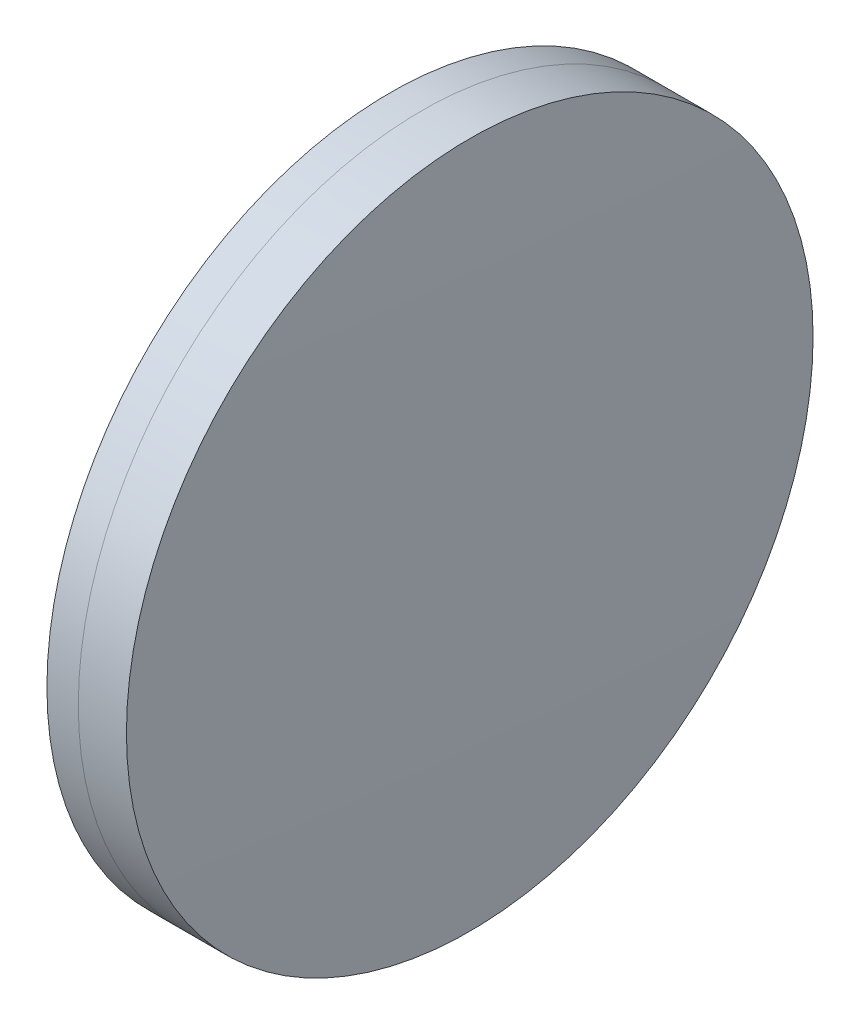
SolidWorks part; units mm, degrees
ref_plane "前视基准面" through (0, 0, 0) normal (0, 0, 1) x (1, 0, 0)
ref_plane "上视基准面" through (0, 0, 0) normal (0, 1, 0) x (1, 0, 0)
ref_plane "右视基准面" through (0, 0, 0) normal (1, 0, 0) x (0, 0, -1)
sketch "草图1" plane through (0, 0, 0) normal (0, 1, 0) x (1, 0, 0)
  line L0 (124.5233, 0) -> (746.023, 0) construction
  line L1 (713.6122, -25.4) -> (715.934, -25.4)
  line L2 (713.6122, 25.4) -> (715.934, 25.4)
  arc A0 (715.934, -25.4) -> (715.934, 25.4) centre (457.7806, 0) ccw
  arc A1 (713.6122, 25.4) -> (713.6122, -25.4) centre (1059.3806, 0) ccw
  point P4 (746.023, 0)
  point P10 (712.6806, 0)
  point P11 (717.1806, 0)
  dimension "D3" = 346.7
  dimension "D4" = 259.4
  dimension "D1" = 25.4
  dimension "D2" = 25.4
  dimension "D5" = 4.5
revolve "旋转1" add sketch "草图1" angle 360 about L0
sketch "草图2" plane through (0, 0, 0) normal (0, 1, 0) x (1, 0, 0)
  line L0 (-0.5519, 0) -> (779.9324, 0) construction
  line L2 (715.934, 25.4) -> (719.4957, 25.4)
  line L3 (715.934, -25.4) -> (719.4957, -25.4)
  arc A0 (719.4957, -25.4) -> (719.4957, 25.4) centre (-412.6194, 0) ccw
  arc A1 (715.934, -25.4) -> (715.934, 25.4) centre (457.7806, 0) ccw construction
  arc A2 (715.934, -25.4) -> (715.934, 25.4) centre (457.7806, 0) ccw
  point P4 (717.1806, 0)
  point P8 (719.7806, 0)
  point P9 (779.9324, 0)
  dimension "D1" = 1132.4
  dimension "D2" = 2.6
revolve "旋转3" add sketch "草图2" angle 360 about L0
